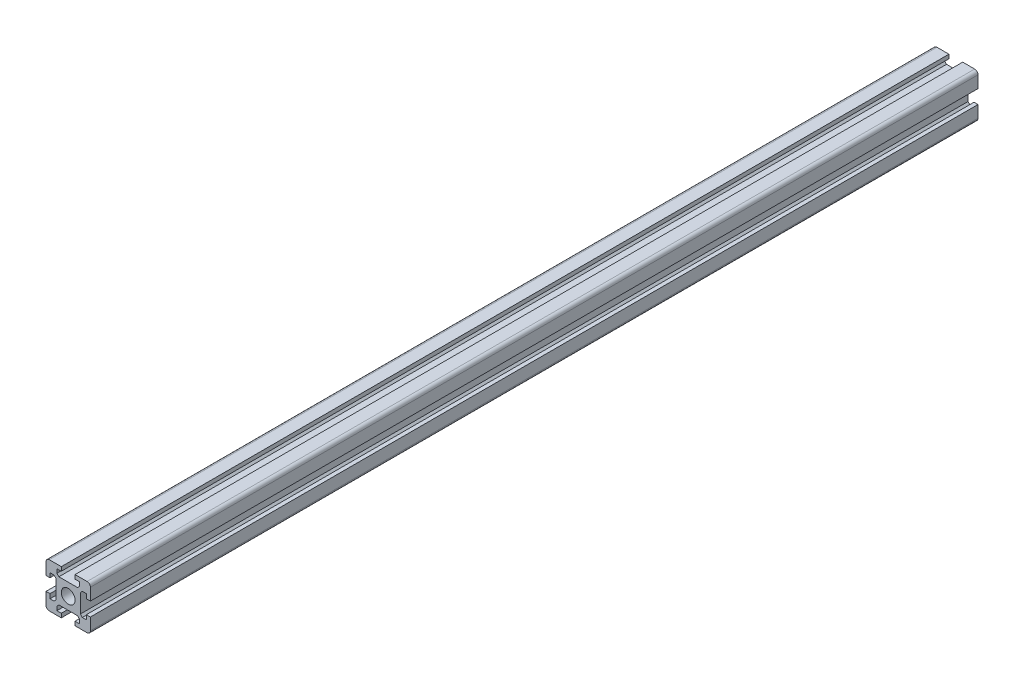
SolidWorks part; units mm, degrees
material "6061 Alloy"
ref_plane "Front Plane" through (0, 0, 0) normal (0, 0, 1) x (1, 0, 0)
ref_plane "Top Plane" through (0, 0, 0) normal (0, 1, 0) x (1, 0, 0)
ref_plane "Right Plane" through (0, 0, 0) normal (1, 0, 0) x (0, 0, -1)
sketch "Sketch1" plane through (0, 0, 0) normal (0, 0, 1) x (1, 0, 0)
  line L0 (-10, 3.1) -> (-8.2, 3.1)
  line L1 (-8.5, 10) -> (-3.1, 10) construction
  line L2 (-10, 8.5) -> (-10, 3.1) construction
  line L3 (-10, -3.1) -> (-10, -8.5) construction
  line L4 (-8.5, -10) -> (-3.1, -10) construction
  line L5 (-10, -3.1) -> (-10, -8.5)
  line L6 (-8.5, -10) -> (-3.1, -10)
  line L7 (-8.2, 3.1) -> (-8.2, 5.1)
  line L8 (-8.2, 5.1) -> (-6.4, 5.1)
  line L9 (-10, -3.1) -> (-8.2, -3.1)
  line L10 (-8.2, -3.1) -> (-8.2, -5.1)
  line L11 (-8.2, -5.1) -> (-6.4, -5.1)
  line L13 (-6.4, 5.1) -> (-5.4929, 4.1929)
  line L14 (-5.4929, 4.1929) -> (-5.4929, -4.1929)
  line L15 (-6.4, -5.1) -> (-5.4929, -4.1929)
  line L16 (-3.1, 10) -> (-3.1, 8.2)
  line L17 (-3.1, 8.2) -> (-5.1, 8.2)
  line L19 (-5.1, 8.2) -> (-5.1, 6.4)
  line L20 (-5.1, 6.4) -> (-4.1929, 5.4929)
  line L21 (-4.1929, 5.4929) -> (4.1929, 5.4929)
  line L22 (4.1929, 5.4929) -> (5.1, 6.4)
  line L23 (5.1, 6.4) -> (5.1, 8.2)
  line L24 (5.1, 8.2) -> (3.1, 8.2)
  line L25 (3.1, 8.2) -> (3.1, 10)
  line L26 (-3.1, -10) -> (-3.1, -8.2)
  line L27 (-3.1, -8.2) -> (-5.1, -8.2)
  line L28 (-5.1, -8.2) -> (-5.1, -6.4)
  line L29 (-5.1, -6.4) -> (-4.1929, -5.4929)
  line L30 (-4.1929, -5.4929) -> (4.1929, -5.4929)
  line L31 (4.1929, -5.4929) -> (5.1, -6.4)
  line L32 (5.1, -6.4) -> (5.1, -8.2)
  line L33 (5.1, -8.2) -> (3.1, -8.2)
  line L34 (3.1, -8.2) -> (3.1, -10)
  line L35 (3.1, -10) -> (8.5, -10)
  line L36 (10, -8.5) -> (10, -3.1)
  line L37 (10, -3.1) -> (8.2, -3.1)
  line L38 (8.2, -3.1) -> (8.2, -5.1)
  line L39 (8.2, -5.1) -> (6.4, -5.1)
  line L40 (6.4, -5.1) -> (5.4929, -4.1929)
  line L41 (5.4929, -4.1929) -> (5.4929, 4.1929)
  line L42 (5.4929, 4.1929) -> (6.4, 5.1)
  line L43 (6.4, 5.1) -> (8.2, 5.1)
  line L44 (8.2, 5.1) -> (8.2, 3.1)
  line L45 (8.2, 3.1) -> (10, 3.1)
  line L46 (10, 3.1) -> (10, 8.5)
  line L47 (8.5, 10) -> (3.1, 10)
  line L48 (-3.1, 10) -> (-8.5, 10)
  line L49 (-10, 8.5) -> (-10, 3.1)
  arc A0 (-8.5, 10) -> (-10, 8.5) centre (-8.5, 8.5) ccw
  arc A1 (-10, -8.5) -> (-8.5, -10) centre (-8.5, -8.5) ccw construction
  arc A2 (8.5, -10) -> (10, -8.5) centre (8.5, -8.5) ccw
  arc A3 (8.5, 10) -> (10, 8.5) centre (8.5, 8.5) cw
  arc A4 (-8.5, -10) -> (-10, -8.5) centre (-8.5, -8.5) cw
  circle A6 centre (0, 0) radius 3.1
  point P0 (0, 0)
  point P44 (-5.2, -3.4858)
  point P47 (-5.2, 3.4858)
  dimension "D3" = 5.4929
  dimension "D5" = 1.5
  dimension "D1" = 6.2
  dimension "D2" = 5.4929
  dimension "D4" = 1.5
  dimension "D6" = 1.5
extrude "Boss-Extrude1" add sketch "Sketch1" along normal blind 400
